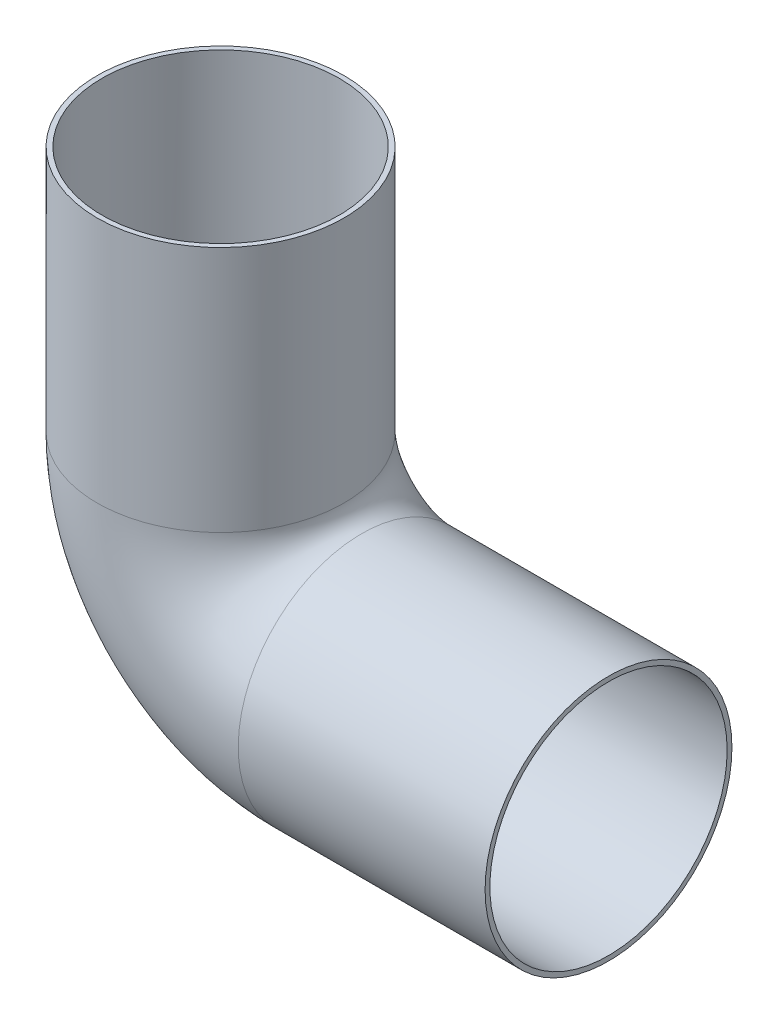
SolidWorks part; units mm, degrees
material "PVC 0.007 Plasticized"
ref_plane "Front Plane" through (0, 0, 0) normal (0, 0, 1) x (1, 0, 0)
ref_plane "Top Plane" through (0, 0, 0) normal (0, 1, 0) x (1, 0, 0)
ref_plane "Right Plane" through (0, 0, 0) normal (1, 0, 0) x (0, 0, -1)
sketch "Sketch1" plane through (0, 0, 0) normal (0, 0, 1) x (1, 0, 0)
  line L0 (-17.4625, 17.7928) -> (-17.4625, -4.4322)
  line L1 (-4.7625, -17.1322) -> (17.4625, -17.1322)
  arc A0 (-17.4625, -4.4322) -> (-4.7625, -17.1322) centre (-4.7625, -4.4322) ccw
  dimension "D1" = 12.7
  dimension "D2" = 34.925
  dimension "D4" = 34.925
  dimension "D5" = 17.4625
ref_plane "Plane1" through (17.4625, -17.1322, 0) normal (1, 0, 0) x (0, 0, -1)
sketch "Sketch2" plane through (17.4625, -17.1322, 0) normal (1, 0, 0) x (0, 0, -1)
  circle A0 centre (0, 0) radius 11.1125
  circle A1 centre (0, 0) radius 10.6807
  dimension "D1" = 22.225
  dimension "D2" = 21.3614
sweep "Sweep1" add profiles "Sketch2" path "Sketch1"
sketch "Sketch3" plane through (17.4625, -17.1322, 0) normal (1, 0, 0) x (0, 0, -1)
  circle A0 centre (0, 0) radius 10.6934
  circle A1 centre (0, 0) radius 10.6807 construction
  dimension "D1" = 21.3868
extrude "Cut-Extrude1" [suppressed] cut sketch "Sketch3" against normal blind 6.35
